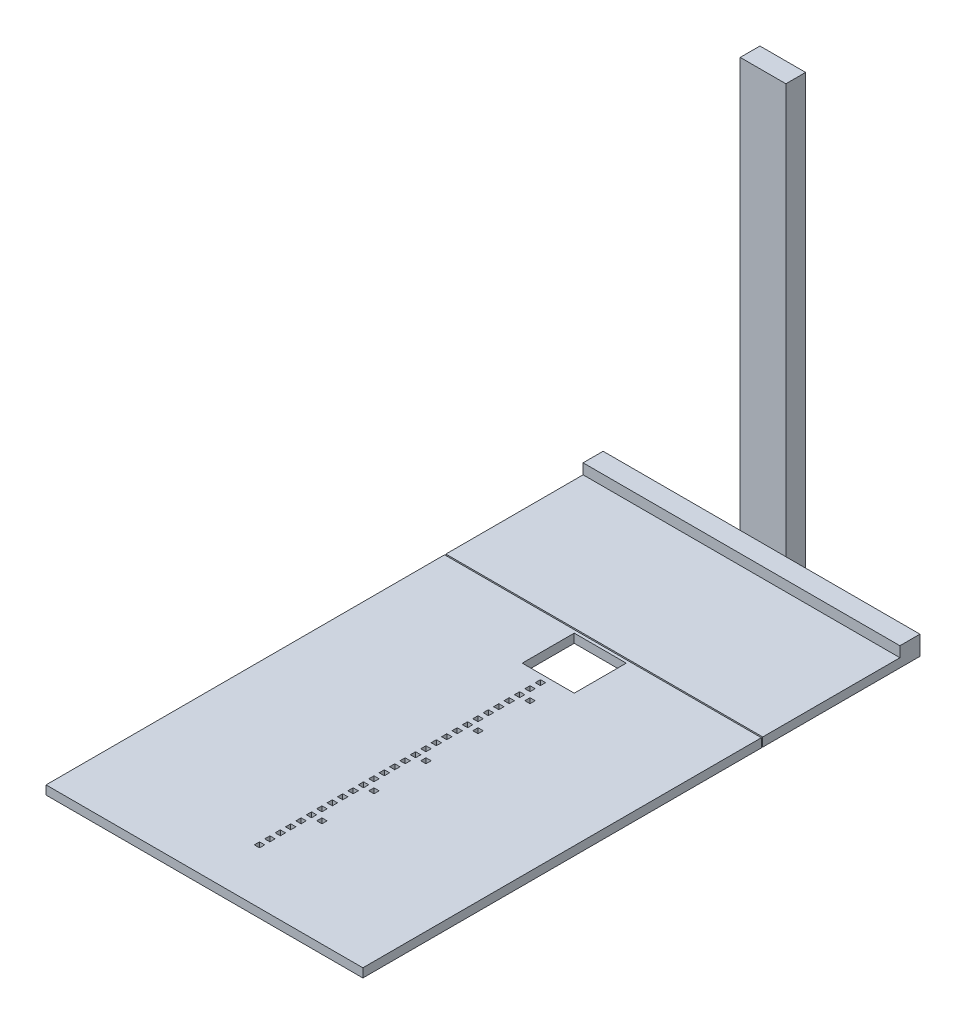
SolidWorks part; units mm, degrees
ref_plane "Front Plane" through (0, 0, 0) normal (0, 0, 1) x (1, 0, 0)
ref_plane "Top Plane" through (0, 0, 0) normal (0, 1, 0) x (1, 0, 0)
ref_plane "Right Plane" through (0, 0, 0) normal (1, 0, 0) x (0, 0, -1)
sketch "Sketch1" plane through (0, 0, 0) normal (0, 1, 0) x (1, 0, 0)
  line L0 (-5, -90) -> (5, -90)
  line L1 (-305, 55.73) -> (304, 55.73)
  line L2 (-305, 55.73) -> (-305, -710.27)
  line L3 (-305, -710.27) -> (304, -710.27)
  line L4 (304, 55.73) -> (304, -710.27)
  line L5 (-50, 50) -> (50, 50)
  line L6 (-50, 50) -> (-50, -50)
  line L7 (-50, -50) -> (50, -50)
  line L8 (50, 50) -> (50, -50)
  line L9 (-5, -60) -> (5, -60)
  line L10 (-5, -60) -> (-5, -70)
  line L11 (-5, -70) -> (5, -70)
  line L12 (5, -60) -> (5, -70)
  line L13 (5, -80) -> (5, -90)
  line L14 (-5, -80) -> (5, -80)
  line L15 (-5, -80) -> (-5, -90)
  line L16 (-5, -110) -> (5, -110)
  line L17 (5, -100) -> (5, -110)
  line L18 (-5, -100) -> (5, -100)
  line L19 (-5, -100) -> (-5, -110)
  line L20 (-5, -130) -> (5, -130)
  line L21 (5, -120) -> (5, -130)
  line L22 (-5, -120) -> (5, -120)
  line L23 (-5, -120) -> (-5, -130)
  line L24 (-5, -150) -> (5, -150)
  line L25 (5, -140) -> (5, -150)
  line L26 (-5, -140) -> (5, -140)
  line L27 (-5, -140) -> (-5, -150)
  line L28 (-5, -170) -> (5, -170)
  line L29 (5, -160) -> (5, -170)
  line L30 (-5, -160) -> (5, -160)
  line L31 (-5, -160) -> (-5, -170)
  line L32 (-5, -190) -> (5, -190)
  line L33 (5, -180) -> (5, -190)
  line L34 (-5, -180) -> (5, -180)
  line L35 (-5, -180) -> (-5, -190)
  line L36 (-5, -210) -> (5, -210)
  line L37 (5, -200) -> (5, -210)
  line L38 (-5, -200) -> (5, -200)
  line L39 (-5, -200) -> (-5, -210)
  line L40 (-5, -230) -> (5, -230)
  line L41 (5, -220) -> (5, -230)
  line L42 (-5, -220) -> (5, -220)
  line L43 (-5, -220) -> (-5, -230)
  line L44 (-5, -250) -> (5, -250)
  line L45 (5, -240) -> (5, -250)
  line L46 (-5, -240) -> (5, -240)
  line L47 (-5, -240) -> (-5, -250)
  line L48 (-5, -270) -> (5, -270)
  line L49 (5, -260) -> (5, -270)
  line L50 (-5, -260) -> (5, -260)
  line L51 (-5, -260) -> (-5, -270)
  line L52 (-5, -290) -> (5, -290)
  line L53 (5, -280) -> (5, -290)
  line L54 (-5, -280) -> (5, -280)
  line L55 (-5, -280) -> (-5, -290)
  line L56 (-5, -310) -> (5, -310)
  line L57 (5, -300) -> (5, -310)
  line L58 (-5, -300) -> (5, -300)
  line L59 (-5, -300) -> (-5, -310)
  line L60 (-5, -330) -> (5, -330)
  line L61 (5, -320) -> (5, -330)
  line L62 (-5, -320) -> (5, -320)
  line L63 (-5, -320) -> (-5, -330)
  line L64 (-5, -350) -> (5, -350)
  line L65 (5, -340) -> (5, -350)
  line L66 (-5, -340) -> (5, -340)
  line L67 (-5, -340) -> (-5, -350)
  line L68 (-5, -370) -> (5, -370)
  line L69 (5, -360) -> (5, -370)
  line L70 (-5, -360) -> (5, -360)
  line L71 (-5, -360) -> (-5, -370)
  line L72 (-5, -390) -> (5, -390)
  line L73 (5, -380) -> (5, -390)
  line L74 (-5, -380) -> (5, -380)
  line L75 (-5, -380) -> (-5, -390)
  line L76 (-5, -410) -> (5, -410)
  line L77 (5, -400) -> (5, -410)
  line L78 (-5, -400) -> (5, -400)
  line L79 (-5, -400) -> (-5, -410)
  line L80 (-5, -430) -> (5, -430)
  line L81 (5, -420) -> (5, -430)
  line L82 (-5, -420) -> (5, -420)
  line L83 (-5, -420) -> (-5, -430)
  line L84 (-5, -450) -> (5, -450)
  line L85 (5, -440) -> (5, -450)
  line L86 (-5, -440) -> (5, -440)
  line L87 (-5, -440) -> (-5, -450)
  line L88 (-5, -470) -> (5, -470)
  line L89 (5, -460) -> (5, -470)
  line L90 (-5, -460) -> (5, -460)
  line L91 (-5, -460) -> (-5, -470)
  line L92 (-5, -490) -> (5, -490)
  line L93 (5, -480) -> (5, -490)
  line L94 (-5, -480) -> (5, -480)
  line L95 (-5, -480) -> (-5, -490)
  line L96 (-5, -510) -> (5, -510)
  line L97 (5, -500) -> (5, -510)
  line L98 (-5, -500) -> (5, -500)
  line L99 (-5, -500) -> (-5, -510)
  line L100 (-5, -530) -> (5, -530)
  line L101 (5, -520) -> (5, -530)
  line L102 (-5, -520) -> (5, -520)
  line L103 (-5, -520) -> (-5, -530)
  line L104 (-5, -550) -> (5, -550)
  line L105 (5, -540) -> (5, -550)
  line L106 (-5, -540) -> (5, -540)
  line L107 (-5, -540) -> (-5, -550)
  line L108 (-5, -570) -> (5, -570)
  line L109 (5, -560) -> (5, -570)
  line L110 (-5, -560) -> (5, -560)
  line L111 (-5, -560) -> (-5, -570)
  line L112 (-5, -590) -> (5, -590)
  line L113 (5, -580) -> (5, -590)
  line L114 (-5, -580) -> (5, -580)
  line L115 (-5, -580) -> (-5, -590)
  line L116 (-5, -610) -> (5, -610)
  line L117 (5, -600) -> (5, -610)
  line L118 (-5, -600) -> (5, -600)
  line L119 (-5, -600) -> (-5, -610)
  line L121 (15, -100) -> (25, -100)
  line L122 (15, -100) -> (15, -110)
  line L123 (25, -100) -> (25, -110)
  line L124 (15, -110) -> (25, -110)
  line L125 (15, -200) -> (25, -200)
  line L126 (15, -200) -> (15, -210)
  line L127 (15, -210) -> (25, -210)
  line L128 (25, -200) -> (25, -210)
  line L129 (15, -300) -> (25, -300)
  line L130 (15, -300) -> (15, -310)
  line L131 (25, -300) -> (25, -310)
  line L132 (15, -310) -> (25, -310)
  line L133 (15, -400) -> (25, -400)
  line L134 (25, -400) -> (25, -410)
  line L135 (15, -410) -> (25, -410)
  line L136 (15, -400) -> (15, -410)
  line L137 (15, -500) -> (25, -500)
  line L138 (25, -500) -> (25, -510)
  line L139 (15, -510) -> (25, -510)
  line L140 (15, -500) -> (15, -510)
  dimension "D1" = 609
  dimension "D2" = 766
  dimension "D3" = 100
  dimension "D4" = 100
  dimension "D5" = 50
  dimension "D6" = 50
  dimension "D7" = 5.73
  dimension "D8" = 255
  dimension "D9" = 10
  dimension "D10" = 10
  dimension "D11" = 60
  dimension "D12" = 5
  dimension "D14" = 80
  dimension "D15" = 2
  dimension "D16" = 100
  dimension "D17" = 10
  dimension "D19" = 100
  dimension "D20" = 10
  dimension "D22" = 100
  dimension "D23" = 10
  dimension "D24" = 2
  dimension "D25" = 100
  dimension "D26" = 10
  dimension "D28" = 100
  dimension "D29" = 10
  dimension "D13" = 28
  dimension "D18" = 2
  dimension "D21" = 2
  dimension "D27" = 2
extrude "Boss-Extrude1" add sketch "Sketch1" along normal blind 17
sketch "Sketch2" plane through (0, 0, 0) normal (0, -1, 0) x (-1, 0, 0)
  line L0 (-304, 55.73) -> (305, 55.73) construction
  line L1 (-304, 360.53) -> (305, 360.53)
  line L2 (-304, 360.53) -> (-304, 58.27)
  line L3 (-304, 58.27) -> (305, 58.27)
  line L4 (305, 360.53) -> (305, 58.27)
  line L6 (305, 55.73) -> (305, -710.27) construction
  dimension "D1" = 2.54
  dimension "D2" = 302.26
  dimension "D3" = 609
extrude "Boss-Extrude2" add sketch "Sketch2" against normal up to surface (17 mm away) separate body up to face at (20, 17, 405)
sketch "Sketch3" plane through (0, 17, 0) normal (0, 1, 0) x (1, 0, 0)
  line L0 (-305, 58.27) -> (-305, 360.53) construction
  line L1 (304, 360.53) -> (-305, 360.53)
  line L2 (304, 360.53) -> (304, 322.03)
  line L3 (304, 322.03) -> (-305, 322.03)
  line L4 (-305, 360.53) -> (-305, 322.03)
  dimension "D1" = 38.5
extrude "Boss-Extrude3" add sketch "Sketch3" along normal blind 20
sketch "Sketch4" plane through (0, 0, 0) normal (0, -1, 0) x (1, 0, 0)
  line L0 (-305, -360.53) -> (304, -360.53) construction
  line L1 (-41.475, -360.53) -> (46.325, -360.53)
  line L2 (-41.475, -360.53) -> (-41.475, -398.43)
  line L3 (-41.475, -398.43) -> (46.325, -398.43)
  line L4 (46.325, -360.53) -> (46.325, -398.43)
  line L5 (-305, -58.27) -> (-305, -360.53) construction
  dimension "D1" = 37.9
  dimension "D2" = 87.8
  dimension "D3" = 263.525
extrude "Boss-Extrude4" add sketch "Sketch4" against normal blind 824.4
